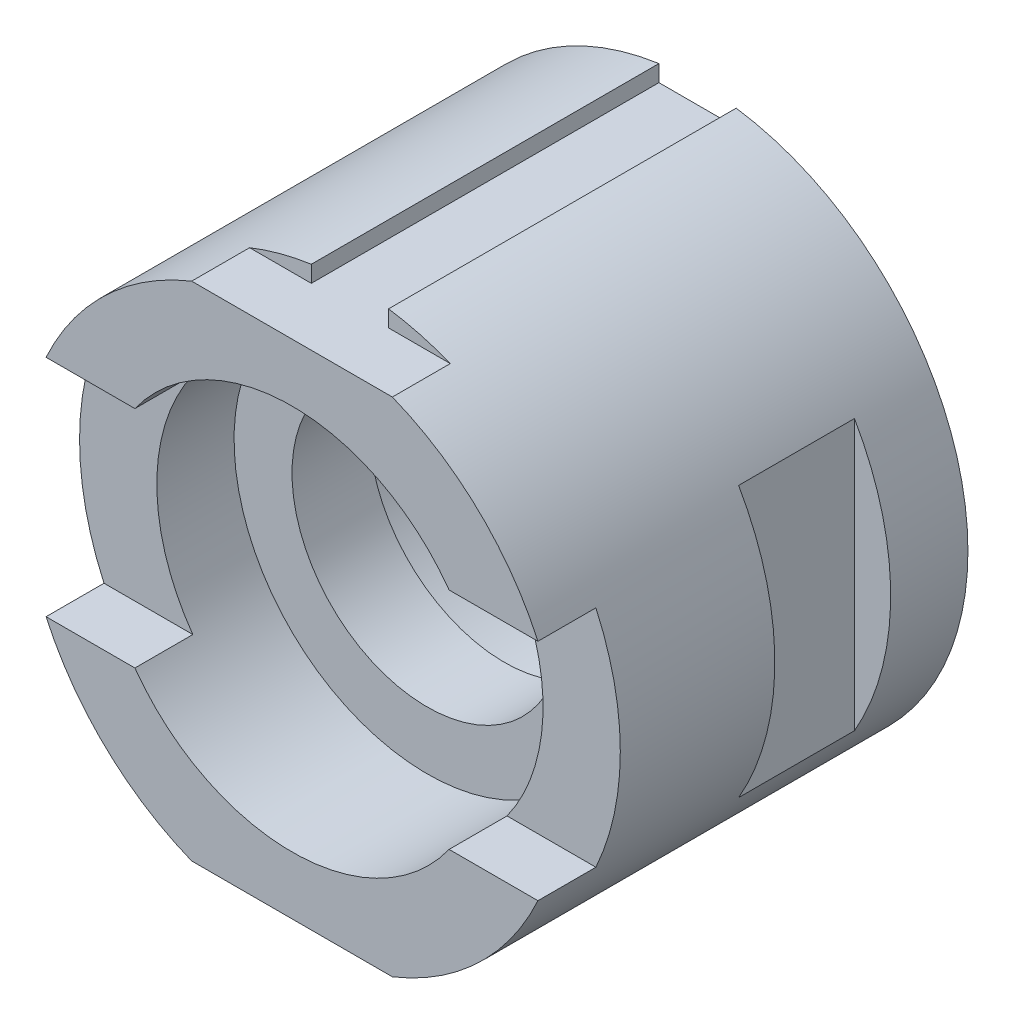
SolidWorks part; units mm, degrees
ref_plane "Front Plane" through (0, 0, 0) normal (0, 0, 1) x (1, 0, 0)
ref_plane "Top Plane" through (0, 0, 0) normal (0, 1, 0) x (1, 0, 0)
ref_plane "Right Plane" through (0, 0, 0) normal (1, 0, 0) x (0, 0, -1)
sketch "Sketch1" plane through (0, 0, 0) normal (0, 0, 1) x (1, 0, 0)
  circle A0 centre (0, 0) radius 35
  dimension "D1" = 70
extrude "Boss-Extrude1" add sketch "Sketch1" along normal blind 10
sketch "Sketch2" plane through (0, 0, 10) normal (0, 0, 1) x (1, 0, 0)
  line L0 (-30.3109, 17.5) -> (-30.3109, -17.5)
  circle A0 centre (0, 0) radius 35 construction
  arc A1 (-30.3109, 17.5) -> (-30.3109, -17.5) centre (0, 0) cw
  dimension "D1" = 35
  dimension "D2" = 35
extrude "Boss-Extrude3" add sketch "Sketch2" along normal blind 15
sketch "Sketch3" plane through (0, 0, 25) normal (0, 0, 1) x (1, 0, 0)
  circle A0 centre (0, 0) radius 25
  dimension "D1" = 50
extrude "Cut-Extrude1" cut sketch "Sketch3" against normal blind 58
sketch "Sketch4" plane through (0, 0, 25) normal (0, 0, 1) x (1, 0, 0)
  circle A0 centre (0, 0) radius 35
  dimension "D1" = 70
extrude "Boss-Extrude5" add sketch "Sketch4" along normal blind 10
sketch "Sketch8" plane through (0, 0, 35) normal (0, 0, 1) x (1, 0, 0)
  circle A0 centre (0, 0) radius 17.5
  dimension "D1" = 35
extrude "Cut-Extrude4" cut sketch "Sketch8" against normal blind 201.5
sketch "Sketch9" plane through (0, 0, 35) normal (0, 0, 1) x (1, 0, 0)
  circle A0 centre (0, 0) radius 35
  circle A1 centre (0, 0) radius 25
  arc A2 (-30.3109, 17.5) -> (-30.3109, -17.5) centre (0, 0) ccw construction
  dimension "D1" = 50
  dimension "D2" = 70
extrude "Boss-Extrude7" add sketch "Sketch9" along normal blind 10
sketch "Sketch10" plane through (0, 0, 45) normal (0, 0, 1) x (1, 0, 0)
  line L0 (-31.837, 14.5399) -> (-20.337, 14.5399)
  line L1 (20.337, 14.5399) -> (31.837, 14.5399)
  line L2 (-31.837, -14.5399) -> (-20.337, -14.5399)
  line L3 (20.337, -14.5399) -> (31.837, -14.5399)
  circle A0 centre (0, 0) radius 35 construction
  circle A1 centre (0, 0) radius 25 construction
  circle A2 centre (0, 0) radius 25 construction
  arc A3 (-20.337, 14.5399) -> (20.337, 14.5399) centre (0, 0) cw
  arc A4 (-31.837, 14.5399) -> (31.837, 14.5399) centre (0, 0) cw
  arc A5 (-20.337, -14.5399) -> (20.337, -14.5399) centre (0, 0) ccw
  arc A6 (-31.837, -14.5399) -> (31.837, -14.5399) centre (0, 0) ccw
  dimension "D1" = 11.5
  dimension "D2" = 25
  dimension "D3" = 35
  dimension "D5" = 25
  dimension "D6" = 35
  dimension "D4" = 11.5
  dimension "D7" = 11.5
extrude "Boss-Extrude8" add sketch "Sketch10" along normal blind 7.5
sketch "Sketch11" plane through (0, 0, 52.5) normal (0, 0, 1) x (1, 0, 0)
  line L0 (-12.9904, -32.5) -> (12.9904, -32.5)
  line L1 (-12.9904, 32.5) -> (12.9904, 32.5)
  arc A0 (-31.837, -14.5399) -> (31.837, -14.5399) centre (0, 0) ccw construction
  arc A1 (-12.9904, -32.5) -> (12.9904, -32.5) centre (0, 0) ccw
  arc A2 (31.837, 14.5399) -> (-31.837, 14.5399) centre (0, 0) ccw construction
  arc A3 (-12.9904, 32.5) -> (12.9904, 32.5) centre (0, 0) cw
  dimension "D1" = 32.5
  dimension "D2" = 32.5
extrude "Cut-Extrude5" cut sketch "Sketch11" against normal blind 7.5
sketch "Sketch19" plane through (0, 0, 45) normal (0, 0, 1) x (1, 0, 0)
  line L0 (-5, 34.641) -> (-5, 32.5)
  line L2 (-12.9904, 32.5) -> (12.9904, 32.5) construction
  line L3 (-5, 32.5) -> (5, 32.5)
  line L4 (5, 32.5) -> (5, 34.641)
  arc A1 (12.9904, 32.5) -> (-12.9904, 32.5) centre (0, 0) ccw construction
  arc A2 (-5, 34.641) -> (5, 34.641) centre (0, 0) cw
  point P10 (0, 32.5)
  dimension "D1" = 35
  dimension "D2" = 10
extrude "Cut-Extrude15" cut sketch "Sketch19" against normal blind 91
sketch "Sketch20" plane through (0, 0, 45) normal (0, 0, 1) x (1, 0, 0)
  line L0 (-5, -34.641) -> (-5, -32.5)
  line L1 (12.9904, -32.5) -> (-12.9904, -32.5) construction
  line L2 (-5, -32.5) -> (5, -32.5)
  line L3 (5, -32.5) -> (5, -34.641)
  arc A0 (-12.9904, -32.5) -> (12.9904, -32.5) centre (0, 0) ccw construction
  arc A1 (-5, -34.641) -> (5, -34.641) centre (0, 0) ccw
  dimension "D1" = 35
  dimension "D2" = 10
extrude "Cut-Extrude16" cut sketch "Sketch20" against normal blind 91
sketch "Sketch21" plane through (0, 0, 0) normal (0, 1, 0) x (1, 0, 0)
  line L0 (-30.3109, -25) -> (-35, -25) construction
  line L1 (-35, -10) -> (-30.3109, -10) construction
  line L2 (-30.3109, -25) -> (-30.3109, -10) construction
  line L3 (-30.3109, -25) -> (-35, -25)
  line L4 (-35, -10) -> (-30.3109, -10)
  line L5 (-30.3109, -25) -> (-30.3109, -10)
  line L6 (0, 0) -> (0, -16.401) construction
  line L7 (30.3109, -25) -> (35, -25)
  line L8 (-35, -10) -> (-30.3109, -10)
  line L9 (-35, -10) -> (-35, -25)
  line L10 (-35, -25) -> (-30.3109, -25)
  line L11 (-30.3109, -10) -> (-30.3109, -25)
  line L12 (35, -10) -> (30.3109, -10)
  line L13 (30.3109, -25) -> (30.3109, -10)
  line L14 (35, -10) -> (35, -25)
extrude "Cut-Extrude17" cut sketch "Sketch21" against normal blind 30 and the other way blind 40 contours L14 L12 L13 L7
